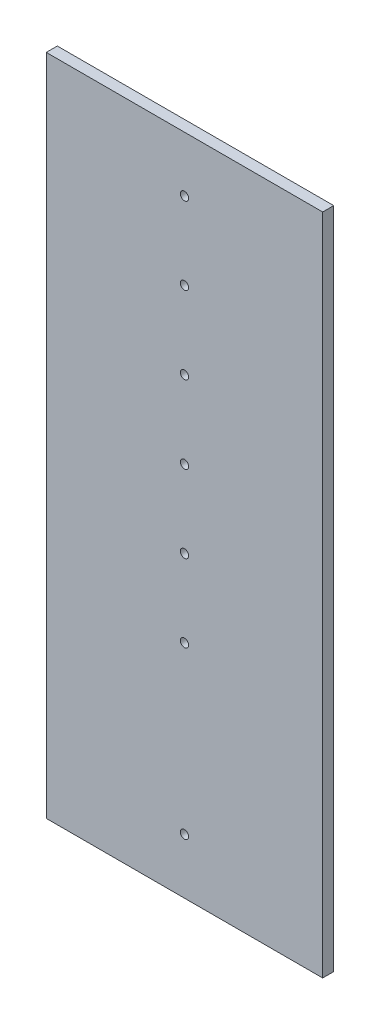
SolidWorks part; units mm, degrees
ref_plane "Front Plane" through (0, 0, 0) normal (0, 0, 1) x (1, 0, 0)
ref_plane "Top Plane" through (0, 0, 0) normal (0, 1, 0) x (1, 0, 0)
ref_plane "Right Plane" through (0, 0, 0) normal (1, 0, 0) x (0, 0, -1)
sketch "Sketch1" plane through (0, 0, 0) normal (0, 0, 1) x (1, 0, 0)
  line L0 (25, 0) -> (25, 20) construction
  line L1 (0, 0) -> (50, 0)
  line L2 (0, 0) -> (0, 120)
  line L3 (0, 120) -> (50, 120)
  line L4 (50, 0) -> (50, 120)
  line L5 (0, 20) -> (50, 20) construction
  line L6 (25, 20) -> (25, 40) construction
  line L7 (25, 40) -> (50, 40) construction
  line L8 (25, 40) -> (25, 54) construction
  line L9 (25, 54) -> (25, 68) construction
  line L10 (25, 68) -> (25, 82) construction
  line L11 (25, 82) -> (25, 96) construction
  line L12 (25, 96) -> (25, 110) construction
  line L13 (25, 0) -> (25, 10) construction
  line L14 (25, 10) -> (50, 10) construction
  circle A0 centre (25, 10) radius 1.5
  circle A1 centre (25, 40) radius 1.5
  circle A2 centre (25, 54) radius 1.5
  circle A3 centre (25, 68) radius 1.5
  circle A4 centre (25.0034, 81.8788) radius 1.5
  circle A5 centre (25.0034, 81.8788) radius 1.5
  circle A6 centre (25.0034, 81.8788) radius 1.5
  circle A7 centre (25, 96) radius 1.5
  circle A8 centre (25, 110) radius 1.5
  point P21 (25.5302, 34.4609)
  point P22 (25, 39.3867)
  point P24 (25, 53.4211)
  point P26 (24.2019, 68)
  point P34 (25.6904, 96)
  point P36 (0, 0)
  point P37 (26.1143, 110)
sketch "Sketch2" plane through (0, 0, 0) normal (0, 0, 1) x (1, 0, 0)
  line L0 (25, 0) -> (25, 10) construction
  line L1 (25, 0) -> (25, 20) construction
  line L2 (25, 10) -> (25, 40) construction
  line L3 (25, 40) -> (25, 54) construction
  line L4 (25, 54) -> (25, 68) construction
  line L5 (25, 68) -> (25, 82) construction
  line L6 (25, 82) -> (25, 96) construction
  line L7 (25, 96) -> (25, 110) construction
  circle A0 centre (25, 110) radius 0.75
  circle A1 centre (25, 96) radius 0.75
  circle A2 centre (25, 82) radius 0.75
  circle A3 centre (25, 68) radius 0.75
  circle A4 centre (25, 54) radius 0.75
  circle A5 centre (25, 40) radius 0.75
  circle A6 centre (25, 10) radius 0.75
  point P18 (0, 0)
  point P21 (26.5, 96)
  point P23 (25.0034, 83.3788)
  point P25 (26.5, 68)
  point P27 (26.5, 54)
  point P29 (25, 38.5)
  point P31 (25, 11.5)
extrude "Boss-Extrude2" add sketch "Sketch1" along normal blind 2 contours L2 L1 L4 L3
extrude "Cut-Extrude2" cut sketch "Sketch2" along normal blind 2
